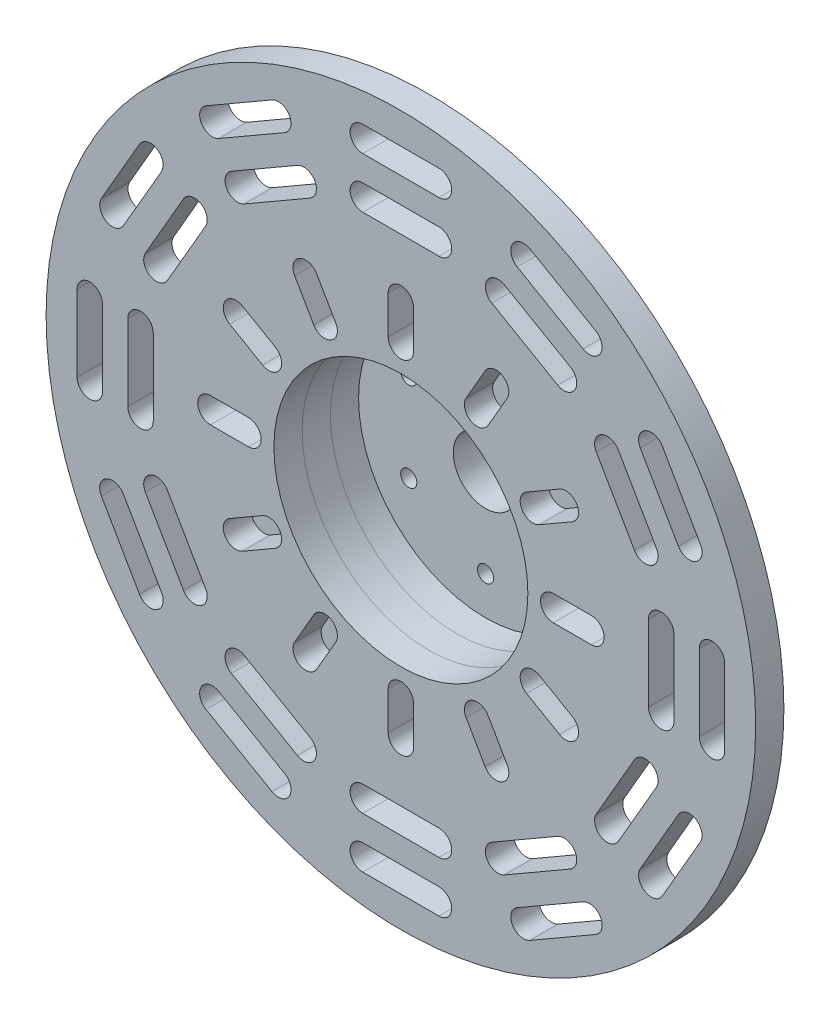
SolidWorks part; units mm, degrees
ref_plane "Front Plane" through (0, 0, 0) normal (0, 0, 1) x (1, 0, 0)
ref_plane "Top Plane" through (0, 0, 0) normal (0, 1, 0) x (1, 0, 0)
ref_plane "Right Plane" through (0, 0, 0) normal (1, 0, 0) x (0, 0, -1)
sketch "Sketch1" plane through (0, 0, 0) normal (0, 0, 1) x (1, 0, 0)
  line L0 (0, -75) -> (0, -60) construction
  line L1 (-5, -75) -> (-5, -60)
  line L2 (5, -75) -> (5, -60)
  line L3 (0, -60) -> (0, 0) construction
  line L4 (-15, -122.5) -> (15, -122.5) construction
  line L7 (-15, -117.5) -> (15, -117.5)
  line L10 (-15, -127.5) -> (15, -127.5)
  line L13 (0, -102.5) -> (0, -122.5) construction
  line L16 (-37.5, -64.9519) -> (-30, -51.9615) construction
  line L19 (-41.8301, -62.4519) -> (-34.3301, -49.4615)
  line L22 (-33.1699, -67.4519) -> (-25.6699, -54.4615)
  line L25 (-64.2404, -81.2676) -> (-38.2596, -96.2676) construction
  line L28 (-61.7404, -76.9375) -> (-35.7596, -91.9375)
  line L31 (-15, -102.5) -> (15, -102.5) construction
  line L32 (-15, -97.5) -> (15, -97.5)
  line L33 (-15, -107.5) -> (15, -107.5)
  line L34 (0, -67.5) -> (0, -102.5) construction
  line L35 (-66.7404, -85.5977) -> (-40.7596, -100.5977)
  line L38 (-74.2404, -98.5881) -> (-48.2596, -113.5881) construction
  line L41 (-71.7404, -94.258) -> (-45.7596, -109.258)
  line L44 (-76.7404, -102.9182) -> (-50.7596, -117.9182)
  line L47 (-64.9519, -37.5) -> (-51.9615, -30) construction
  line L50 (-67.4519, -33.1699) -> (-54.4615, -25.6699)
  line L53 (-62.4519, -41.8301) -> (-49.4615, -34.3301)
  line L56 (-96.2676, -38.2596) -> (-81.2676, -64.2404) construction
  line L59 (-91.9375, -35.7596) -> (-76.9375, -61.7404)
  line L62 (-100.5977, -40.7596) -> (-85.5977, -66.7404)
  line L63 (-113.5881, -48.2596) -> (-98.5881, -74.2404) construction
  line L64 (-109.258, -45.7596) -> (-94.258, -71.7404)
  line L65 (-117.9182, -50.7596) -> (-102.9182, -76.7404)
  line L66 (-75, 0) -> (-60, 0) construction
  line L67 (-75, 5) -> (-60, 5)
  line L68 (-75, -5) -> (-60, -5)
  line L69 (-102.5, 15) -> (-102.5, -15) construction
  line L70 (-97.5, 15) -> (-97.5, -15)
  line L71 (-107.5, 15) -> (-107.5, -15)
  line L72 (-122.5, 15) -> (-122.5, -15) construction
  line L73 (-117.5, 15) -> (-117.5, -15)
  line L74 (-127.5, 15) -> (-127.5, -15)
  line L75 (-64.9519, 37.5) -> (-51.9615, 30) construction
  line L76 (-62.4519, 41.8301) -> (-49.4615, 34.3301)
  line L77 (-67.4519, 33.1699) -> (-54.4615, 25.6699)
  line L78 (-81.2676, 64.2404) -> (-96.2676, 38.2596) construction
  line L79 (-76.9375, 61.7404) -> (-91.9375, 35.7596)
  line L80 (-85.5977, 66.7404) -> (-100.5977, 40.7596)
  line L81 (-98.5881, 74.2404) -> (-113.5881, 48.2596) construction
  line L82 (-94.258, 71.7404) -> (-109.258, 45.7596)
  line L83 (-102.9182, 76.7404) -> (-117.9182, 50.7596)
  line L84 (-37.5, 64.9519) -> (-30, 51.9615) construction
  line L85 (-33.1699, 67.4519) -> (-25.6699, 54.4615)
  line L86 (-41.8301, 62.4519) -> (-34.3301, 49.4615)
  line L87 (-38.2596, 96.2676) -> (-64.2404, 81.2676) construction
  line L88 (-35.7596, 91.9375) -> (-61.7404, 76.9375)
  line L89 (-40.7596, 100.5977) -> (-66.7404, 85.5977)
  line L90 (-48.2596, 113.5881) -> (-74.2404, 98.5881) construction
  line L91 (-45.7596, 109.258) -> (-71.7404, 94.258)
  line L92 (-50.7596, 117.9182) -> (-76.7404, 102.9182)
  line L93 (0, 75) -> (0, 60) construction
  line L94 (5, 75) -> (5, 60)
  line L95 (-5, 75) -> (-5, 60)
  line L96 (15, 102.5) -> (-15, 102.5) construction
  line L97 (15, 97.5) -> (-15, 97.5)
  line L98 (15, 107.5) -> (-15, 107.5)
  line L99 (15, 122.5) -> (-15, 122.5) construction
  line L100 (15, 117.5) -> (-15, 117.5)
  line L101 (15, 127.5) -> (-15, 127.5)
  line L102 (37.5, 64.9519) -> (30, 51.9615) construction
  line L103 (41.8301, 62.4519) -> (34.3301, 49.4615)
  line L104 (33.1699, 67.4519) -> (25.6699, 54.4615)
  line L105 (64.2404, 81.2676) -> (38.2596, 96.2676) construction
  line L106 (61.7404, 76.9375) -> (35.7596, 91.9375)
  line L107 (66.7404, 85.5977) -> (40.7596, 100.5977)
  line L108 (74.2404, 98.5881) -> (48.2596, 113.5881) construction
  line L109 (71.7404, 94.258) -> (45.7596, 109.258)
  line L110 (76.7404, 102.9182) -> (50.7596, 117.9182)
  line L111 (64.9519, 37.5) -> (51.9615, 30) construction
  line L112 (67.4519, 33.1699) -> (54.4615, 25.6699)
  line L113 (62.4519, 41.8301) -> (49.4615, 34.3301)
  line L114 (96.2676, 38.2596) -> (81.2676, 64.2404) construction
  line L115 (91.9375, 35.7596) -> (76.9375, 61.7404)
  line L116 (100.5977, 40.7596) -> (85.5977, 66.7404)
  line L117 (113.5881, 48.2596) -> (98.5881, 74.2404) construction
  line L118 (109.258, 45.7596) -> (94.258, 71.7404)
  line L119 (117.9182, 50.7596) -> (102.9182, 76.7404)
  line L120 (75, 0) -> (60, 0) construction
  line L121 (75, -5) -> (60, -5)
  line L122 (75, 5) -> (60, 5)
  line L123 (102.5, -15) -> (102.5, 15) construction
  line L124 (97.5, -15) -> (97.5, 15)
  line L125 (107.5, -15) -> (107.5, 15)
  line L126 (122.5, -15) -> (122.5, 15) construction
  line L127 (117.5, -15) -> (117.5, 15)
  line L128 (127.5, -15) -> (127.5, 15)
  line L129 (64.9519, -37.5) -> (51.9615, -30) construction
  line L130 (62.4519, -41.8301) -> (49.4615, -34.3301)
  line L131 (67.4519, -33.1699) -> (54.4615, -25.6699)
  line L132 (81.2676, -64.2404) -> (96.2676, -38.2596) construction
  line L133 (76.9375, -61.7404) -> (91.9375, -35.7596)
  line L134 (85.5977, -66.7404) -> (100.5977, -40.7596)
  line L135 (98.5881, -74.2404) -> (113.5881, -48.2596) construction
  line L136 (94.258, -71.7404) -> (109.258, -45.7596)
  line L137 (102.9182, -76.7404) -> (117.9182, -50.7596)
  line L138 (37.5, -64.9519) -> (30, -51.9615) construction
  line L139 (33.1699, -67.4519) -> (25.6699, -54.4615)
  line L140 (41.8301, -62.4519) -> (34.3301, -49.4615)
  line L141 (38.2596, -96.2676) -> (64.2404, -81.2676) construction
  line L142 (35.7596, -91.9375) -> (61.7404, -76.9375)
  line L143 (40.7596, -100.5977) -> (66.7404, -85.5977)
  line L144 (48.2596, -113.5881) -> (74.2404, -98.5881) construction
  line L145 (45.7596, -109.258) -> (71.7404, -94.258)
  line L146 (50.7596, -117.9182) -> (76.7404, -102.9182)
  circle A0 centre (0, 0) radius 139.7
  circle A1 centre (0, 0) radius 25
  arc A2 (-5, -75) -> (5, -75) centre (0, -75) ccw
  arc A3 (5, -60) -> (-5, -60) centre (0, -60) ccw
  arc A22 (-15, -97.5) -> (-15, -107.5) centre (-15, -102.5) ccw
  arc A23 (15, -107.5) -> (15, -97.5) centre (15, -102.5) ccw
  arc A42 (-15, -117.5) -> (-15, -127.5) centre (-15, -122.5) ccw
  arc A43 (15, -127.5) -> (15, -117.5) centre (15, -122.5) ccw
  arc A44 (-41.8301, -62.4519) -> (-33.1699, -67.4519) centre (-37.5, -64.9519) ccw
  arc A45 (-25.6699, -54.4615) -> (-34.3301, -49.4615) centre (-30, -51.9615) ccw
  arc A46 (-61.7404, -76.9375) -> (-66.7404, -85.5977) centre (-64.2404, -81.2676) ccw
  arc A47 (-40.7596, -100.5977) -> (-35.7596, -91.9375) centre (-38.2596, -96.2676) ccw
  arc A48 (-71.7404, -94.258) -> (-76.7404, -102.9182) centre (-74.2404, -98.5881) ccw
  arc A49 (-50.7596, -117.9182) -> (-45.7596, -109.258) centre (-48.2596, -113.5881) ccw
  arc A50 (-67.4519, -33.1699) -> (-62.4519, -41.8301) centre (-64.9519, -37.5) ccw
  arc A51 (-49.4615, -34.3301) -> (-54.4615, -25.6699) centre (-51.9615, -30) ccw
  arc A52 (-91.9375, -35.7596) -> (-100.5977, -40.7596) centre (-96.2676, -38.2596) ccw
  arc A53 (-85.5977, -66.7404) -> (-76.9375, -61.7404) centre (-81.2676, -64.2404) ccw
  arc A54 (-109.258, -45.7596) -> (-117.9182, -50.7596) centre (-113.5881, -48.2596) ccw
  arc A55 (-102.9182, -76.7404) -> (-94.258, -71.7404) centre (-98.5881, -74.2404) ccw
  arc A56 (-75, 5) -> (-75, -5) centre (-75, 0) ccw
  arc A57 (-60, -5) -> (-60, 5) centre (-60, 0) ccw
  arc A58 (-97.5, 15) -> (-107.5, 15) centre (-102.5, 15) ccw
  arc A59 (-107.5, -15) -> (-97.5, -15) centre (-102.5, -15) ccw
  arc A60 (-117.5, 15) -> (-127.5, 15) centre (-122.5, 15) ccw
  arc A61 (-127.5, -15) -> (-117.5, -15) centre (-122.5, -15) ccw
  arc A62 (-62.4519, 41.8301) -> (-67.4519, 33.1699) centre (-64.9519, 37.5) ccw
  arc A63 (-54.4615, 25.6699) -> (-49.4615, 34.3301) centre (-51.9615, 30) ccw
  arc A64 (-76.9375, 61.7404) -> (-85.5977, 66.7404) centre (-81.2676, 64.2404) ccw
  arc A65 (-100.5977, 40.7596) -> (-91.9375, 35.7596) centre (-96.2676, 38.2596) ccw
  arc A66 (-94.258, 71.7404) -> (-102.9182, 76.7404) centre (-98.5881, 74.2404) ccw
  arc A67 (-117.9182, 50.7596) -> (-109.258, 45.7596) centre (-113.5881, 48.2596) ccw
  arc A68 (-33.1699, 67.4519) -> (-41.8301, 62.4519) centre (-37.5, 64.9519) ccw
  arc A69 (-34.3301, 49.4615) -> (-25.6699, 54.4615) centre (-30, 51.9615) ccw
  arc A70 (-35.7596, 91.9375) -> (-40.7596, 100.5977) centre (-38.2596, 96.2676) ccw
  arc A71 (-66.7404, 85.5977) -> (-61.7404, 76.9375) centre (-64.2404, 81.2676) ccw
  arc A72 (-45.7596, 109.258) -> (-50.7596, 117.9182) centre (-48.2596, 113.5881) ccw
  arc A73 (-76.7404, 102.9182) -> (-71.7404, 94.258) centre (-74.2404, 98.5881) ccw
  arc A74 (5, 75) -> (-5, 75) centre (0, 75) ccw
  arc A75 (-5, 60) -> (5, 60) centre (0, 60) ccw
  arc A76 (15, 97.5) -> (15, 107.5) centre (15, 102.5) ccw
  arc A77 (-15, 107.5) -> (-15, 97.5) centre (-15, 102.5) ccw
  arc A78 (15, 117.5) -> (15, 127.5) centre (15, 122.5) ccw
  arc A79 (-15, 127.5) -> (-15, 117.5) centre (-15, 122.5) ccw
  arc A80 (41.8301, 62.4519) -> (33.1699, 67.4519) centre (37.5, 64.9519) ccw
  arc A81 (25.6699, 54.4615) -> (34.3301, 49.4615) centre (30, 51.9615) ccw
  arc A82 (61.7404, 76.9375) -> (66.7404, 85.5977) centre (64.2404, 81.2676) ccw
  arc A83 (40.7596, 100.5977) -> (35.7596, 91.9375) centre (38.2596, 96.2676) ccw
  arc A84 (71.7404, 94.258) -> (76.7404, 102.9182) centre (74.2404, 98.5881) ccw
  arc A85 (50.7596, 117.9182) -> (45.7596, 109.258) centre (48.2596, 113.5881) ccw
  arc A86 (67.4519, 33.1699) -> (62.4519, 41.8301) centre (64.9519, 37.5) ccw
  arc A87 (49.4615, 34.3301) -> (54.4615, 25.6699) centre (51.9615, 30) ccw
  arc A88 (91.9375, 35.7596) -> (100.5977, 40.7596) centre (96.2676, 38.2596) ccw
  arc A89 (85.5977, 66.7404) -> (76.9375, 61.7404) centre (81.2676, 64.2404) ccw
  arc A90 (109.258, 45.7596) -> (117.9182, 50.7596) centre (113.5881, 48.2596) ccw
  arc A91 (102.9182, 76.7404) -> (94.258, 71.7404) centre (98.5881, 74.2404) ccw
  arc A92 (75, -5) -> (75, 5) centre (75, 0) ccw
  arc A93 (60, 5) -> (60, -5) centre (60, 0) ccw
  arc A94 (97.5, -15) -> (107.5, -15) centre (102.5, -15) ccw
  arc A95 (107.5, 15) -> (97.5, 15) centre (102.5, 15) ccw
  arc A96 (117.5, -15) -> (127.5, -15) centre (122.5, -15) ccw
  arc A97 (127.5, 15) -> (117.5, 15) centre (122.5, 15) ccw
  arc A98 (62.4519, -41.8301) -> (67.4519, -33.1699) centre (64.9519, -37.5) ccw
  arc A99 (54.4615, -25.6699) -> (49.4615, -34.3301) centre (51.9615, -30) ccw
  arc A100 (76.9375, -61.7404) -> (85.5977, -66.7404) centre (81.2676, -64.2404) ccw
  arc A101 (100.5977, -40.7596) -> (91.9375, -35.7596) centre (96.2676, -38.2596) ccw
  arc A102 (94.258, -71.7404) -> (102.9182, -76.7404) centre (98.5881, -74.2404) ccw
  arc A103 (117.9182, -50.7596) -> (109.258, -45.7596) centre (113.5881, -48.2596) ccw
  arc A104 (33.1699, -67.4519) -> (41.8301, -62.4519) centre (37.5, -64.9519) ccw
  arc A105 (34.3301, -49.4615) -> (25.6699, -54.4615) centre (30, -51.9615) ccw
  arc A106 (35.7596, -91.9375) -> (40.7596, -100.5977) centre (38.2596, -96.2676) ccw
  arc A107 (66.7404, -85.5977) -> (61.7404, -76.9375) centre (64.2404, -81.2676) ccw
  arc A108 (45.7596, -109.258) -> (50.7596, -117.9182) centre (48.2596, -113.5881) ccw
  arc A109 (76.7404, -102.9182) -> (71.7404, -94.258) centre (74.2404, -98.5881) ccw
  point P6 (0, -67.5)
  point P14 (0, -102.5)
  point P17 (0, -122.5)
  point P29 (-33.75, -58.4567)
  point P36 (-51.25, -88.7676)
  point P39 (-61.25, -106.0881)
  point P51 (-58.4567, -33.75)
  point P60 (-88.7676, -51.25)
  point P63 (-106.0881, -61.25)
  point P75 (-67.5, 0)
  point P78 (-25.429, 35)
  point P89 (-102.5, 0)
  point P93 (-122.5, 0)
  point P105 (-58.4567, 33.75)
  point P113 (-88.7676, 51.25)
  point P116 (-106.0881, 61.25)
  point P127 (-33.75, 58.4567)
  point P135 (-51.25, 88.7676)
  point P138 (-61.25, 106.0881)
  point P151 (0, 67.5)
  point P158 (0, 102.5)
  point P161 (0, 122.5)
  point P172 (33.75, 58.4567)
  point P179 (51.25, 88.7676)
  point P182 (61.25, 106.0881)
  point P193 (58.4567, 33.75)
  point P200 (88.7676, 51.25)
  point P203 (106.0881, 61.25)
  point P214 (67.5, 0)
  point P221 (102.5, 0)
  point P224 (122.5, 0)
  point P235 (58.4567, -33.75)
  point P242 (88.7676, -51.25)
  point P245 (106.0881, -61.25)
  point P256 (33.75, -58.4567)
  point P263 (51.25, -88.7676)
  point P266 (61.25, -106.0881)
  point P275 (0, 0)
  dimension "D1" = 279.4
  dimension "D2" = 50
  dimension "D3" = 60
  dimension "D4" = 15
  dimension "D5" = 10
  dimension "D7" = 30
  dimension "D8" = 10
  dimension "D9" = 35
  dimension "D6" = 20
  dimension "D10" = 12
sketch "Sketch4" plane through (0, 0, 0) normal (0, 0, 1) x (1, 0, 0)
  circle A0 centre (0, 0) radius 12.7
  circle A1 centre (0, 0) radius 75
  circle A2 centre (30.2459, 17.4625) radius 3.175 construction
  circle A3 centre (-30.2459, 17.4625) radius 3.175 construction
  circle A4 centre (0, -34.925) radius 3.175 construction
  circle A5 centre (30.2459, 17.4625) radius 3.175
  circle A6 centre (-30.2459, 17.4625) radius 3.175
  circle A7 centre (0, -34.925) radius 3.175
  arc A8 (-2.2451, 37.1701) -> (0.3966, 38.0751) centre (0, 34.925) ccw construction
  arc A9 (0.3966, 38.0751) -> (-2.2451, 37.1701) centre (0, 34.925) ccw construction
  arc A10 (-2.2451, 37.1701) -> (0.3966, 38.0751) centre (0, 34.925) ccw
  arc A11 (0.3966, 38.0751) -> (-2.2451, 37.1701) centre (0, 34.925) ccw
  arc A12 (-31.0677, -20.5293) -> (-33.1723, -18.6941) centre (-30.2459, -17.4625) ccw construction
  arc A13 (-33.1723, -18.6941) -> (-31.0677, -20.5293) centre (-30.2459, -17.4625) ccw construction
  arc A14 (-31.0677, -20.5293) -> (-33.1723, -18.6941) centre (-30.2459, -17.4625) ccw
  arc A15 (-33.1723, -18.6941) -> (-31.0677, -20.5293) centre (-30.2459, -17.4625) ccw
  arc A16 (33.3128, -16.6407) -> (32.7757, -19.381) centre (30.2459, -17.4625) ccw construction
  arc A17 (32.7757, -19.381) -> (33.3128, -16.6407) centre (30.2459, -17.4625) ccw construction
  arc A18 (33.3128, -16.6407) -> (32.7757, -19.381) centre (30.2459, -17.4625) ccw
  arc A19 (32.7757, -19.381) -> (33.3128, -16.6407) centre (30.2459, -17.4625) ccw
  dimension "D1" = 150
  dimension "D2" = 25.4
extrude "Boss-Extrude1" add sketch "Sketch4" along normal blind 11.1125
sketch "Sketch5" plane through (0, 0, 11.1125) normal (0, 0, 1) x (1, 0, 0)
  circle A0 centre (0, 0) radius 50
  circle A1 centre (0, 0) radius 75
  dimension "D1" = 100
  dimension "D2" = 150
extrude "Boss-Extrude2" add sketch "Sketch5" along normal blind 11.1125 separate body
sketch "Sketch6" plane through (0, 0, 22.225) normal (0, 0, 1) x (1, 0, 0)
  circle A0 centre (0, 0) radius 50
  circle A1 centre (0, 0) radius 90
  dimension "D1" = 180
  dimension "D2" = 100
extrude "Boss-Extrude3" add sketch "Sketch6" along normal blind 11.1125
sketch "Sketch7" plane through (0, 0, 33.3375) normal (0, 0, 1) x (1, 0, 0)
  line L2 (-5, -60) -> (-5, -75)
  line L3 (5, -75) -> (5, -60)
  line L4 (-5, -60) -> (-5, -75)
  line L5 (5, -75) -> (5, -60)
  line L6 (15, -117.5) -> (-15, -117.5)
  line L7 (-15, -127.5) -> (15, -127.5)
  line L8 (15, -117.5) -> (-15, -117.5)
  line L9 (-15, -127.5) -> (15, -127.5)
  line L10 (-45.7596, -109.258) -> (-71.7404, -94.258)
  line L11 (-76.7404, -102.9182) -> (-50.7596, -117.9182)
  line L12 (-45.7596, -109.258) -> (-71.7404, -94.258)
  line L13 (-76.7404, -102.9182) -> (-50.7596, -117.9182)
  line L14 (-33.1699, -67.4519) -> (-25.6699, -54.4615)
  line L15 (-34.3301, -49.4615) -> (-41.8301, -62.4519)
  line L16 (-33.1699, -67.4519) -> (-25.6699, -54.4615)
  line L17 (-34.3301, -49.4615) -> (-41.8301, -62.4519)
  line L18 (-54.4615, -25.6699) -> (-67.4519, -33.1699)
  line L19 (-62.4519, -41.8301) -> (-49.4615, -34.3301)
  line L20 (-54.4615, -25.6699) -> (-67.4519, -33.1699)
  line L21 (-62.4519, -41.8301) -> (-49.4615, -34.3301)
  line L22 (-35.7596, -91.9375) -> (-61.7404, -76.9375)
  line L23 (-66.7404, -85.5977) -> (-40.7596, -100.5977)
  line L24 (-35.7596, -91.9375) -> (-61.7404, -76.9375)
  line L25 (-66.7404, -85.5977) -> (-40.7596, -100.5977)
  line L26 (-94.258, -71.7404) -> (-109.258, -45.7596)
  line L27 (-117.9182, -50.7596) -> (-102.9182, -76.7404)
  line L28 (-94.258, -71.7404) -> (-109.258, -45.7596)
  line L29 (-117.9182, -50.7596) -> (-102.9182, -76.7404)
  line L30 (-76.9375, -61.7404) -> (-91.9375, -35.7596)
  line L31 (-100.5977, -40.7596) -> (-85.5977, -66.7404)
  line L32 (-76.9375, -61.7404) -> (-91.9375, -35.7596)
  line L33 (-100.5977, -40.7596) -> (-85.5977, -66.7404)
  line L34 (-75, -5) -> (-60, -5)
  line L35 (-60, 5) -> (-75, 5)
  line L36 (-75, -5) -> (-60, -5)
  line L37 (-60, 5) -> (-75, 5)
  line L38 (-15, -107.5) -> (15, -107.5)
  line L39 (15, -97.5) -> (-15, -97.5)
  line L40 (-15, -107.5) -> (15, -107.5)
  line L41 (15, -97.5) -> (-15, -97.5)
  line L42 (-49.4615, 34.3301) -> (-62.4519, 41.8301)
  line L43 (-67.4519, 33.1699) -> (-54.4615, 25.6699)
  line L44 (-49.4615, 34.3301) -> (-62.4519, 41.8301)
  line L45 (-67.4519, 33.1699) -> (-54.4615, 25.6699)
  line L46 (-127.5, 15) -> (-127.5, -15)
  line L47 (-117.5, -15) -> (-117.5, 15)
  line L48 (-127.5, 15) -> (-127.5, -15)
  line L49 (-117.5, -15) -> (-117.5, 15)
  line L50 (-97.5, -15) -> (-97.5, 15)
  line L51 (-107.5, 15) -> (-107.5, -15)
  line L52 (-97.5, -15) -> (-97.5, 15)
  line L53 (-107.5, 15) -> (-107.5, -15)
  line L54 (-109.258, 45.7596) -> (-94.258, 71.7404)
  line L55 (-102.9182, 76.7404) -> (-117.9182, 50.7596)
  line L56 (-109.258, 45.7596) -> (-94.258, 71.7404)
  line L57 (-102.9182, 76.7404) -> (-117.9182, 50.7596)
  line L58 (-91.9375, 35.7596) -> (-76.9375, 61.7404)
  line L59 (-85.5977, 66.7404) -> (-100.5977, 40.7596)
  line L60 (-91.9375, 35.7596) -> (-76.9375, 61.7404)
  line L61 (-85.5977, 66.7404) -> (-100.5977, 40.7596)
  line L62 (-71.7404, 94.258) -> (-45.7596, 109.258)
  line L63 (-50.7596, 117.9182) -> (-76.7404, 102.9182)
  line L64 (-71.7404, 94.258) -> (-45.7596, 109.258)
  line L65 (-50.7596, 117.9182) -> (-76.7404, 102.9182)
  line L66 (-25.6699, 54.4615) -> (-33.1699, 67.4519)
  line L67 (-41.8301, 62.4519) -> (-34.3301, 49.4615)
  line L68 (-25.6699, 54.4615) -> (-33.1699, 67.4519)
  line L69 (-41.8301, 62.4519) -> (-34.3301, 49.4615)
  line L70 (5, 60) -> (5, 75)
  line L71 (-5, 75) -> (-5, 60)
  line L72 (5, 60) -> (5, 75)
  line L73 (-5, 75) -> (-5, 60)
  line L74 (-61.7404, 76.9375) -> (-35.7596, 91.9375)
  line L75 (-40.7596, 100.5977) -> (-66.7404, 85.5977)
  line L76 (-61.7404, 76.9375) -> (-35.7596, 91.9375)
  line L77 (-40.7596, 100.5977) -> (-66.7404, 85.5977)
  line L78 (-15, 117.5) -> (15, 117.5)
  line L79 (15, 127.5) -> (-15, 127.5)
  line L80 (-15, 117.5) -> (15, 117.5)
  line L81 (15, 127.5) -> (-15, 127.5)
  line L82 (-15, 97.5) -> (15, 97.5)
  line L83 (15, 107.5) -> (-15, 107.5)
  line L84 (-15, 97.5) -> (15, 97.5)
  line L85 (15, 107.5) -> (-15, 107.5)
  line L86 (45.7596, 109.258) -> (71.7404, 94.258)
  line L87 (76.7404, 102.9182) -> (50.7596, 117.9182)
  line L88 (45.7596, 109.258) -> (71.7404, 94.258)
  line L89 (76.7404, 102.9182) -> (50.7596, 117.9182)
  line L90 (35.7596, 91.9375) -> (61.7404, 76.9375)
  line L91 (66.7404, 85.5977) -> (40.7596, 100.5977)
  line L92 (35.7596, 91.9375) -> (61.7404, 76.9375)
  line L93 (66.7404, 85.5977) -> (40.7596, 100.5977)
  line L94 (34.3301, 49.4615) -> (41.8301, 62.4519)
  line L95 (33.1699, 67.4519) -> (25.6699, 54.4615)
  line L96 (34.3301, 49.4615) -> (41.8301, 62.4519)
  line L97 (33.1699, 67.4519) -> (25.6699, 54.4615)
  line L98 (94.258, 71.7404) -> (109.258, 45.7596)
  line L99 (117.9182, 50.7596) -> (102.9182, 76.7404)
  line L100 (94.258, 71.7404) -> (109.258, 45.7596)
  line L101 (117.9182, 50.7596) -> (102.9182, 76.7404)
  line L102 (54.4615, 25.6699) -> (67.4519, 33.1699)
  line L103 (62.4519, 41.8301) -> (49.4615, 34.3301)
  line L104 (54.4615, 25.6699) -> (67.4519, 33.1699)
  line L105 (62.4519, 41.8301) -> (49.4615, 34.3301)
  line L106 (60, -5) -> (75, -5)
  line L107 (75, 5) -> (60, 5)
  line L108 (60, -5) -> (75, -5)
  line L109 (75, 5) -> (60, 5)
  line L110 (76.9375, 61.7404) -> (91.9375, 35.7596)
  line L111 (100.5977, 40.7596) -> (85.5977, 66.7404)
  line L112 (76.9375, 61.7404) -> (91.9375, 35.7596)
  line L113 (100.5977, 40.7596) -> (85.5977, 66.7404)
  line L114 (49.4615, -34.3301) -> (62.4519, -41.8301)
  line L115 (67.4519, -33.1699) -> (54.4615, -25.6699)
  line L116 (49.4615, -34.3301) -> (62.4519, -41.8301)
  line L117 (67.4519, -33.1699) -> (54.4615, -25.6699)
  line L118 (117.5, 15) -> (117.5, -15)
  line L119 (127.5, -15) -> (127.5, 15)
  line L120 (117.5, 15) -> (117.5, -15)
  line L121 (127.5, -15) -> (127.5, 15)
  line L122 (97.5, 15) -> (97.5, -15)
  line L123 (107.5, -15) -> (107.5, 15)
  line L124 (97.5, 15) -> (97.5, -15)
  line L125 (107.5, -15) -> (107.5, 15)
  line L126 (109.258, -45.7596) -> (94.258, -71.7404)
  line L127 (102.9182, -76.7404) -> (117.9182, -50.7596)
  line L128 (109.258, -45.7596) -> (94.258, -71.7404)
  line L129 (102.9182, -76.7404) -> (117.9182, -50.7596)
  line L130 (91.9375, -35.7596) -> (76.9375, -61.7404)
  line L131 (85.5977, -66.7404) -> (100.5977, -40.7596)
  line L132 (91.9375, -35.7596) -> (76.9375, -61.7404)
  line L133 (85.5977, -66.7404) -> (100.5977, -40.7596)
  line L134 (71.7404, -94.258) -> (45.7596, -109.258)
  line L135 (50.7596, -117.9182) -> (76.7404, -102.9182)
  line L136 (71.7404, -94.258) -> (45.7596, -109.258)
  line L137 (50.7596, -117.9182) -> (76.7404, -102.9182)
  line L138 (61.7404, -76.9375) -> (35.7596, -91.9375)
  line L139 (40.7596, -100.5977) -> (66.7404, -85.5977)
  line L140 (61.7404, -76.9375) -> (35.7596, -91.9375)
  line L141 (40.7596, -100.5977) -> (66.7404, -85.5977)
  line L142 (25.6699, -54.4615) -> (33.1699, -67.4519)
  line L143 (41.8301, -62.4519) -> (34.3301, -49.4615)
  line L144 (25.6699, -54.4615) -> (33.1699, -67.4519)
  line L145 (41.8301, -62.4519) -> (34.3301, -49.4615)
  circle A0 centre (0, 0) radius 50
  circle A3 centre (0, 0) radius 139.7
  circle A4 centre (0, 0) radius 139.7
  arc A6 (5, -60) -> (-5, -60) centre (0, -60) ccw
  arc A7 (-5, -75) -> (5, -75) centre (0, -75) ccw
  arc A8 (5, -60) -> (-5, -60) centre (0, -60) ccw
  arc A9 (-5, -75) -> (5, -75) centre (0, -75) ccw
  arc A10 (15, -127.5) -> (15, -117.5) centre (15, -122.5) ccw
  arc A11 (-15, -117.5) -> (-15, -127.5) centre (-15, -122.5) ccw
  arc A12 (15, -127.5) -> (15, -117.5) centre (15, -122.5) ccw
  arc A13 (-15, -117.5) -> (-15, -127.5) centre (-15, -122.5) ccw
  arc A14 (-50.7596, -117.9182) -> (-45.7596, -109.258) centre (-48.2596, -113.5881) ccw
  arc A15 (-71.7404, -94.258) -> (-76.7404, -102.9182) centre (-74.2404, -98.5881) ccw
  arc A16 (-50.7596, -117.9182) -> (-45.7596, -109.258) centre (-48.2596, -113.5881) ccw
  arc A17 (-71.7404, -94.258) -> (-76.7404, -102.9182) centre (-74.2404, -98.5881) ccw
  arc A18 (-25.6699, -54.4615) -> (-34.3301, -49.4615) centre (-30, -51.9615) ccw
  arc A19 (-41.8301, -62.4519) -> (-33.1699, -67.4519) centre (-37.5, -64.9519) ccw
  arc A20 (-25.6699, -54.4615) -> (-34.3301, -49.4615) centre (-30, -51.9615) ccw
  arc A21 (-41.8301, -62.4519) -> (-33.1699, -67.4519) centre (-37.5, -64.9519) ccw
  arc A22 (-49.4615, -34.3301) -> (-54.4615, -25.6699) centre (-51.9615, -30) ccw
  arc A23 (-67.4519, -33.1699) -> (-62.4519, -41.8301) centre (-64.9519, -37.5) ccw
  arc A24 (-49.4615, -34.3301) -> (-54.4615, -25.6699) centre (-51.9615, -30) ccw
  arc A25 (-67.4519, -33.1699) -> (-62.4519, -41.8301) centre (-64.9519, -37.5) ccw
  arc A26 (-40.7596, -100.5977) -> (-35.7596, -91.9375) centre (-38.2596, -96.2676) ccw
  arc A27 (-61.7404, -76.9375) -> (-66.7404, -85.5977) centre (-64.2404, -81.2676) ccw
  arc A28 (-40.7596, -100.5977) -> (-35.7596, -91.9375) centre (-38.2596, -96.2676) ccw
  arc A29 (-61.7404, -76.9375) -> (-66.7404, -85.5977) centre (-64.2404, -81.2676) ccw
  arc A30 (-102.9182, -76.7404) -> (-94.258, -71.7404) centre (-98.5881, -74.2404) ccw
  arc A31 (-109.258, -45.7596) -> (-117.9182, -50.7596) centre (-113.5881, -48.2596) ccw
  arc A32 (-102.9182, -76.7404) -> (-94.258, -71.7404) centre (-98.5881, -74.2404) ccw
  arc A33 (-109.258, -45.7596) -> (-117.9182, -50.7596) centre (-113.5881, -48.2596) ccw
  arc A34 (-85.5977, -66.7404) -> (-76.9375, -61.7404) centre (-81.2676, -64.2404) ccw
  arc A35 (-91.9375, -35.7596) -> (-100.5977, -40.7596) centre (-96.2676, -38.2596) ccw
  arc A36 (-85.5977, -66.7404) -> (-76.9375, -61.7404) centre (-81.2676, -64.2404) ccw
  arc A37 (-91.9375, -35.7596) -> (-100.5977, -40.7596) centre (-96.2676, -38.2596) ccw
  arc A38 (-60, -5) -> (-60, 5) centre (-60, 0) ccw
  arc A39 (-75, 5) -> (-75, -5) centre (-75, 0) ccw
  arc A40 (-60, -5) -> (-60, 5) centre (-60, 0) ccw
  arc A41 (-75, 5) -> (-75, -5) centre (-75, 0) ccw
  arc A42 (15, -107.5) -> (15, -97.5) centre (15, -102.5) ccw
  arc A43 (-15, -97.5) -> (-15, -107.5) centre (-15, -102.5) ccw
  arc A44 (15, -107.5) -> (15, -97.5) centre (15, -102.5) ccw
  arc A45 (-15, -97.5) -> (-15, -107.5) centre (-15, -102.5) ccw
  arc A46 (-54.4615, 25.6699) -> (-49.4615, 34.3301) centre (-51.9615, 30) ccw
  arc A47 (-62.4519, 41.8301) -> (-67.4519, 33.1699) centre (-64.9519, 37.5) ccw
  arc A48 (-54.4615, 25.6699) -> (-49.4615, 34.3301) centre (-51.9615, 30) ccw
  arc A49 (-62.4519, 41.8301) -> (-67.4519, 33.1699) centre (-64.9519, 37.5) ccw
  arc A50 (-127.5, -15) -> (-117.5, -15) centre (-122.5, -15) ccw
  arc A51 (-117.5, 15) -> (-127.5, 15) centre (-122.5, 15) ccw
  arc A52 (-127.5, -15) -> (-117.5, -15) centre (-122.5, -15) ccw
  arc A53 (-117.5, 15) -> (-127.5, 15) centre (-122.5, 15) ccw
  arc A54 (-107.5, -15) -> (-97.5, -15) centre (-102.5, -15) ccw
  arc A55 (-97.5, 15) -> (-107.5, 15) centre (-102.5, 15) ccw
  arc A56 (-107.5, -15) -> (-97.5, -15) centre (-102.5, -15) ccw
  arc A57 (-97.5, 15) -> (-107.5, 15) centre (-102.5, 15) ccw
  arc A58 (-117.9182, 50.7596) -> (-109.258, 45.7596) centre (-113.5881, 48.2596) ccw
  arc A59 (-94.258, 71.7404) -> (-102.9182, 76.7404) centre (-98.5881, 74.2404) ccw
  arc A60 (-117.9182, 50.7596) -> (-109.258, 45.7596) centre (-113.5881, 48.2596) ccw
  arc A61 (-94.258, 71.7404) -> (-102.9182, 76.7404) centre (-98.5881, 74.2404) ccw
  arc A62 (-100.5977, 40.7596) -> (-91.9375, 35.7596) centre (-96.2676, 38.2596) ccw
  arc A63 (-76.9375, 61.7404) -> (-85.5977, 66.7404) centre (-81.2676, 64.2404) ccw
  arc A64 (-100.5977, 40.7596) -> (-91.9375, 35.7596) centre (-96.2676, 38.2596) ccw
  arc A65 (-76.9375, 61.7404) -> (-85.5977, 66.7404) centre (-81.2676, 64.2404) ccw
  arc A66 (-76.7404, 102.9182) -> (-71.7404, 94.258) centre (-74.2404, 98.5881) ccw
  arc A67 (-45.7596, 109.258) -> (-50.7596, 117.9182) centre (-48.2596, 113.5881) ccw
  arc A68 (-76.7404, 102.9182) -> (-71.7404, 94.258) centre (-74.2404, 98.5881) ccw
  arc A69 (-45.7596, 109.258) -> (-50.7596, 117.9182) centre (-48.2596, 113.5881) ccw
  arc A70 (-34.3301, 49.4615) -> (-25.6699, 54.4615) centre (-30, 51.9615) ccw
  arc A71 (-33.1699, 67.4519) -> (-41.8301, 62.4519) centre (-37.5, 64.9519) ccw
  arc A72 (-34.3301, 49.4615) -> (-25.6699, 54.4615) centre (-30, 51.9615) ccw
  arc A73 (-33.1699, 67.4519) -> (-41.8301, 62.4519) centre (-37.5, 64.9519) ccw
  arc A74 (-5, 60) -> (5, 60) centre (0, 60) ccw
  arc A75 (5, 75) -> (-5, 75) centre (0, 75) ccw
  arc A76 (-5, 60) -> (5, 60) centre (0, 60) ccw
  arc A77 (5, 75) -> (-5, 75) centre (0, 75) ccw
  arc A78 (-66.7404, 85.5977) -> (-61.7404, 76.9375) centre (-64.2404, 81.2676) ccw
  arc A79 (-35.7596, 91.9375) -> (-40.7596, 100.5977) centre (-38.2596, 96.2676) ccw
  arc A80 (-66.7404, 85.5977) -> (-61.7404, 76.9375) centre (-64.2404, 81.2676) ccw
  arc A81 (-35.7596, 91.9375) -> (-40.7596, 100.5977) centre (-38.2596, 96.2676) ccw
  arc A82 (-15, 127.5) -> (-15, 117.5) centre (-15, 122.5) ccw
  arc A83 (15, 117.5) -> (15, 127.5) centre (15, 122.5) ccw
  arc A84 (-15, 127.5) -> (-15, 117.5) centre (-15, 122.5) ccw
  arc A85 (15, 117.5) -> (15, 127.5) centre (15, 122.5) ccw
  arc A86 (-15, 107.5) -> (-15, 97.5) centre (-15, 102.5) ccw
  arc A87 (15, 97.5) -> (15, 107.5) centre (15, 102.5) ccw
  arc A88 (-15, 107.5) -> (-15, 97.5) centre (-15, 102.5) ccw
  arc A89 (15, 97.5) -> (15, 107.5) centre (15, 102.5) ccw
  arc A90 (50.7596, 117.9182) -> (45.7596, 109.258) centre (48.2596, 113.5881) ccw
  arc A91 (71.7404, 94.258) -> (76.7404, 102.9182) centre (74.2404, 98.5881) ccw
  arc A92 (50.7596, 117.9182) -> (45.7596, 109.258) centre (48.2596, 113.5881) ccw
  arc A93 (71.7404, 94.258) -> (76.7404, 102.9182) centre (74.2404, 98.5881) ccw
  arc A94 (40.7596, 100.5977) -> (35.7596, 91.9375) centre (38.2596, 96.2676) ccw
  arc A95 (61.7404, 76.9375) -> (66.7404, 85.5977) centre (64.2404, 81.2676) ccw
  arc A96 (40.7596, 100.5977) -> (35.7596, 91.9375) centre (38.2596, 96.2676) ccw
  arc A97 (61.7404, 76.9375) -> (66.7404, 85.5977) centre (64.2404, 81.2676) ccw
  arc A98 (25.6699, 54.4615) -> (34.3301, 49.4615) centre (30, 51.9615) ccw
  arc A99 (41.8301, 62.4519) -> (33.1699, 67.4519) centre (37.5, 64.9519) ccw
  arc A100 (25.6699, 54.4615) -> (34.3301, 49.4615) centre (30, 51.9615) ccw
  arc A101 (41.8301, 62.4519) -> (33.1699, 67.4519) centre (37.5, 64.9519) ccw
  arc A102 (102.9182, 76.7404) -> (94.258, 71.7404) centre (98.5881, 74.2404) ccw
  arc A103 (109.258, 45.7596) -> (117.9182, 50.7596) centre (113.5881, 48.2596) ccw
  arc A104 (102.9182, 76.7404) -> (94.258, 71.7404) centre (98.5881, 74.2404) ccw
  arc A105 (109.258, 45.7596) -> (117.9182, 50.7596) centre (113.5881, 48.2596) ccw
  arc A106 (49.4615, 34.3301) -> (54.4615, 25.6699) centre (51.9615, 30) ccw
  arc A107 (67.4519, 33.1699) -> (62.4519, 41.8301) centre (64.9519, 37.5) ccw
  arc A108 (49.4615, 34.3301) -> (54.4615, 25.6699) centre (51.9615, 30) ccw
  arc A109 (67.4519, 33.1699) -> (62.4519, 41.8301) centre (64.9519, 37.5) ccw
  arc A110 (60, 5) -> (60, -5) centre (60, 0) ccw
  arc A111 (75, -5) -> (75, 5) centre (75, 0) ccw
  arc A112 (60, 5) -> (60, -5) centre (60, 0) ccw
  arc A113 (75, -5) -> (75, 5) centre (75, 0) ccw
  arc A114 (85.5977, 66.7404) -> (76.9375, 61.7404) centre (81.2676, 64.2404) ccw
  arc A115 (91.9375, 35.7596) -> (100.5977, 40.7596) centre (96.2676, 38.2596) ccw
  arc A116 (85.5977, 66.7404) -> (76.9375, 61.7404) centre (81.2676, 64.2404) ccw
  arc A117 (91.9375, 35.7596) -> (100.5977, 40.7596) centre (96.2676, 38.2596) ccw
  arc A118 (54.4615, -25.6699) -> (49.4615, -34.3301) centre (51.9615, -30) ccw
  arc A119 (62.4519, -41.8301) -> (67.4519, -33.1699) centre (64.9519, -37.5) ccw
  arc A120 (54.4615, -25.6699) -> (49.4615, -34.3301) centre (51.9615, -30) ccw
  arc A121 (62.4519, -41.8301) -> (67.4519, -33.1699) centre (64.9519, -37.5) ccw
  arc A122 (127.5, 15) -> (117.5, 15) centre (122.5, 15) ccw
  arc A123 (117.5, -15) -> (127.5, -15) centre (122.5, -15) ccw
  arc A124 (127.5, 15) -> (117.5, 15) centre (122.5, 15) ccw
  arc A125 (117.5, -15) -> (127.5, -15) centre (122.5, -15) ccw
  arc A126 (107.5, 15) -> (97.5, 15) centre (102.5, 15) ccw
  arc A127 (97.5, -15) -> (107.5, -15) centre (102.5, -15) ccw
  arc A128 (107.5, 15) -> (97.5, 15) centre (102.5, 15) ccw
  arc A129 (97.5, -15) -> (107.5, -15) centre (102.5, -15) ccw
  arc A130 (117.9182, -50.7596) -> (109.258, -45.7596) centre (113.5881, -48.2596) ccw
  arc A131 (94.258, -71.7404) -> (102.9182, -76.7404) centre (98.5881, -74.2404) ccw
  arc A132 (117.9182, -50.7596) -> (109.258, -45.7596) centre (113.5881, -48.2596) ccw
  arc A133 (94.258, -71.7404) -> (102.9182, -76.7404) centre (98.5881, -74.2404) ccw
  arc A134 (100.5977, -40.7596) -> (91.9375, -35.7596) centre (96.2676, -38.2596) ccw
  arc A135 (76.9375, -61.7404) -> (85.5977, -66.7404) centre (81.2676, -64.2404) ccw
  arc A136 (100.5977, -40.7596) -> (91.9375, -35.7596) centre (96.2676, -38.2596) ccw
  arc A137 (76.9375, -61.7404) -> (85.5977, -66.7404) centre (81.2676, -64.2404) ccw
  arc A138 (76.7404, -102.9182) -> (71.7404, -94.258) centre (74.2404, -98.5881) ccw
  arc A139 (45.7596, -109.258) -> (50.7596, -117.9182) centre (48.2596, -113.5881) ccw
  arc A140 (76.7404, -102.9182) -> (71.7404, -94.258) centre (74.2404, -98.5881) ccw
  arc A141 (45.7596, -109.258) -> (50.7596, -117.9182) centre (48.2596, -113.5881) ccw
  arc A142 (66.7404, -85.5977) -> (61.7404, -76.9375) centre (64.2404, -81.2676) ccw
  arc A143 (35.7596, -91.9375) -> (40.7596, -100.5977) centre (38.2596, -96.2676) ccw
  arc A144 (66.7404, -85.5977) -> (61.7404, -76.9375) centre (64.2404, -81.2676) ccw
  arc A145 (35.7596, -91.9375) -> (40.7596, -100.5977) centre (38.2596, -96.2676) ccw
  arc A146 (34.3301, -49.4615) -> (25.6699, -54.4615) centre (30, -51.9615) ccw
  arc A147 (33.1699, -67.4519) -> (41.8301, -62.4519) centre (37.5, -64.9519) ccw
  arc A148 (34.3301, -49.4615) -> (25.6699, -54.4615) centre (30, -51.9615) ccw
  arc A149 (33.1699, -67.4519) -> (41.8301, -62.4519) centre (37.5, -64.9519) ccw
  circle M147 centre (0, 0) radius 90
  dimension "D2" = 0
  dimension "D3" = 0
  dimension "D4" = 0
  dimension "D5" = 0
  dimension "D6" = 0
  dimension "D7" = 0
  dimension "D8" = 0
  dimension "D9" = 0
  dimension "D10" = 0
  dimension "D11" = 0
  dimension "D12" = 0
  dimension "D13" = 0
  dimension "D14" = 0
  dimension "D15" = 0
  dimension "D16" = 0
  dimension "D17" = 0
  dimension "D18" = 0
  dimension "D19" = 0
  dimension "D20" = 0
  dimension "D21" = 0
  dimension "D22" = 0
  dimension "D23" = 0
  dimension "D24" = 0
  dimension "D25" = 0
  dimension "D26" = 0
  dimension "D27" = 0
  dimension "D28" = 0
  dimension "D29" = 0
  dimension "D30" = 0
  dimension "D31" = 0
  dimension "D32" = 0
  dimension "D33" = 0
  dimension "D34" = 0
  dimension "D35" = 0
  dimension "D36" = 0
  dimension "D37" = 0
  dimension "D38" = 0
extrude "Boss-Extrude4" add sketch "Sketch7" along normal blind 11.1125 separate body contours A4 A145 L140 A144 L141 A141 L136 A140 L137 A137 L132 A136 L133 A133 L128 A132 L129 A129 L124 A128 L125 A125 L120 A124 L121 A117 L112 A116 L113 A105 L100 A104 L101 A97 L92 A96 L93 A93 L88 A92 L89 | A149 L144 A148 L145 A121 L116 A120 L117 A113 L108 A112 L109 A109 L104 A108 L105 A101 L96 A100 L97 A77 L72 A76 L73 A73 L68 A72 L69 A49 L44 A48 L45 A41 L37 A40 L36 A25 L20 A24 L21 M147
